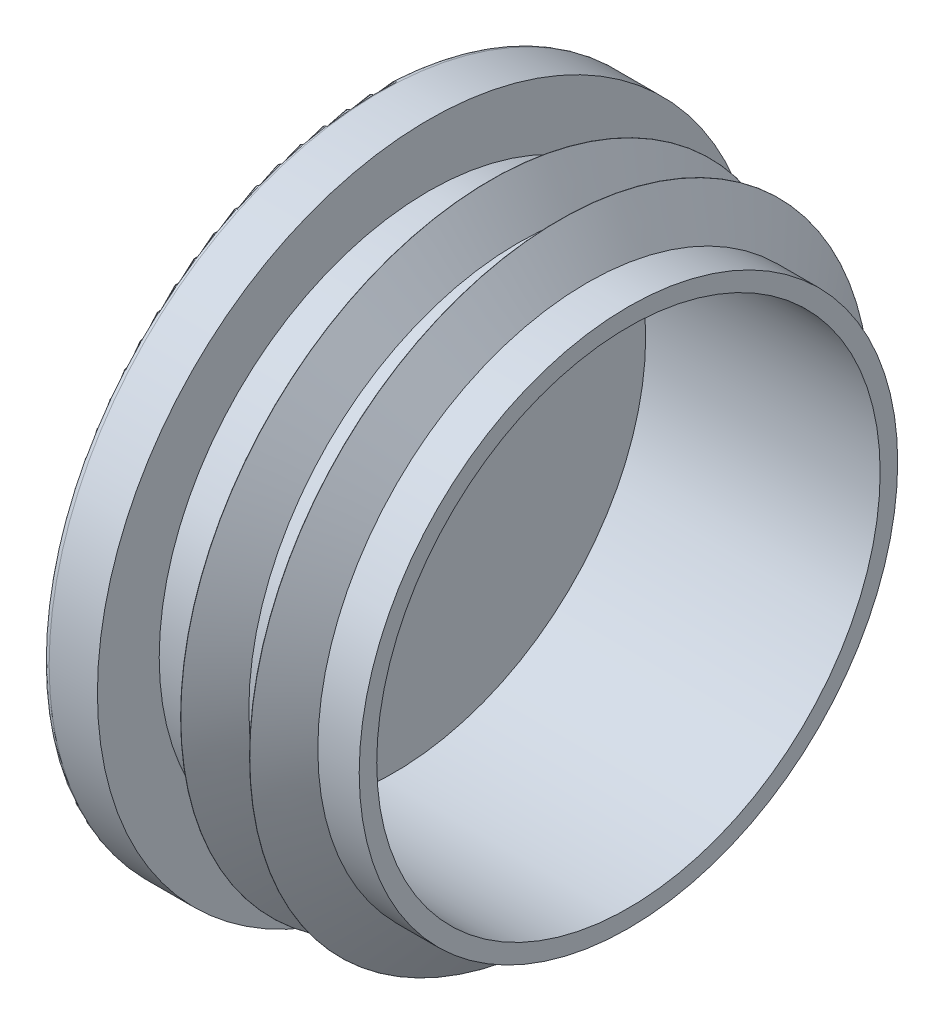
SolidWorks part; units mm, degrees
material "PE High Density"
ref_plane "Front Plane" through (0, 0, 0) normal (0, 0, 1) x (1, 0, 0)
ref_plane "Top Plane" through (0, 0, 0) normal (0, 1, 0) x (1, 0, 0)
ref_plane "Right Plane" through (0, 0, 0) normal (1, 0, 0) x (0, 0, -1)
sketch "Sketch1" plane through (0, 0, 0) normal (0, 0, 1) x (1, 0, 0)
  line L0 (0, 0) -> (21.2671, 0) construction
  line L1 (0, 0) -> (0, 24)
  line L2 (0, 24) -> (4, 24)
  line L3 (4, 24) -> (4, 19.5212)
  line L4 (4, 19.5212) -> (8.5, 19.5212)
  line L5 (8.5, 19.5212) -> (8.5, 22.5)
  line L6 (8.5, 22.5) -> (10.5, 19.5212)
  line L7 (10.5, 19.5212) -> (13.5, 19.5212)
  line L8 (13.5, 19.5212) -> (13.5, 22.5)
  line L9 (13.5, 22.5) -> (15.5, 19.5212)
  line L10 (15.5, 19.5212) -> (18.5, 19.5212)
  line L14 (18.5, 19.5212) -> (18.5, 18.25)
  line L15 (18.5, 18.25) -> (1.5, 18.25)
  line L16 (1.5, 18.25) -> (1.5, 0)
  line L17 (0, 0) -> (1.5, 0)
  line L18 (1.5, 0) -> (1.8035, -0.2125)
  dimension "D1" = 48
  dimension "D2" = 4
  dimension "D3" = 18.5
  dimension "D4" = 36.5
  dimension "D6" = 4.5
  dimension "D7" = 3
  dimension "D9" = 45
  dimension "D10" = 17
revolve "Revolve1" add sketch "Sketch1" angle 360 about L0
fillet "Fillet1" radius 0.01 2 edges at (13.5, 0, 22.5) (8.5, 0, 22.5)
fillet "Fillet2" radius 0.5 1 edges at (0, 0, 24)
